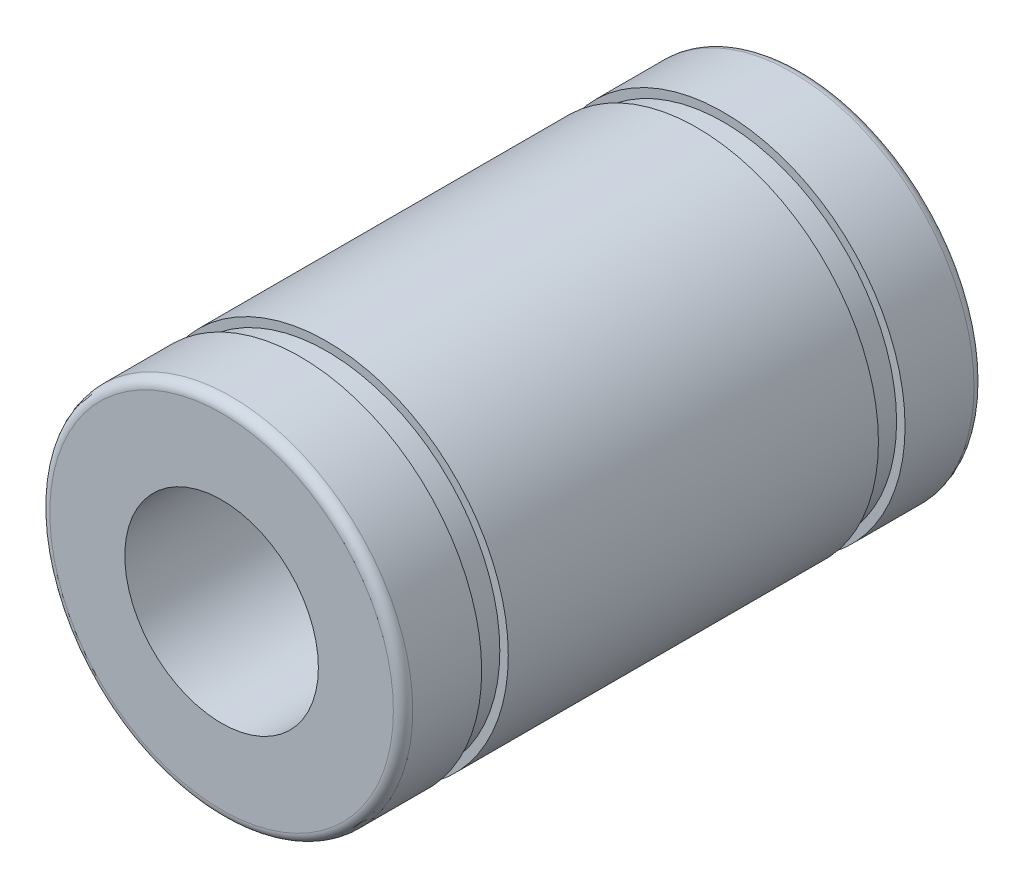
SolidWorks part; units mm, degrees
material "PTFE generico"
ref_plane "Piano frontale" through (0, 0, 0) normal (0, 0, 1) x (1, 0, 0)
ref_plane "Piano superiore" through (0, 0, 0) normal (0, 1, 0) x (1, 0, 0)
ref_plane "Piano destro" through (0, 0, 0) normal (1, 0, 0) x (0, 0, -1)
sketch "Schizzo1" plane through (0, 0, 0) normal (0, 1, 0) x (1, 0, 0)
  line L0 (7.1, -3) -> (4, -3)
  line L1 (4, -3) -> (4, -27)
  line L2 (4, -27) -> (7.1, -27)
  line L3 (7.5, -26.6) -> (7.5, -23.75)
  line L4 (7.5, -23.75) -> (7.15, -23.75)
  line L5 (7.15, -23.75) -> (7.15, -22.65)
  line L6 (7.15, -22.65) -> (7.5, -22.65)
  line L7 (7.5, -22.65) -> (7.5, -7.35)
  line L8 (7.5, -7.35) -> (7.15, -7.35)
  line L9 (7.15, -7.35) -> (7.15, -6.25)
  line L10 (7.15, -6.25) -> (7.5, -6.25)
  line L11 (7.5, -6.25) -> (7.5, -3.4)
  line L12 (0, -2.9987) -> (0, -27.0013) construction
  arc A0 (7.1, -27) -> (7.5, -26.6) centre (7.1, -26.6) ccw
  arc A1 (7.5, -3.4) -> (7.1, -3) centre (7.1, -3.4) ccw
revolve "Rivoluzione1" add sketch "Schizzo1" angle 360 about L12
